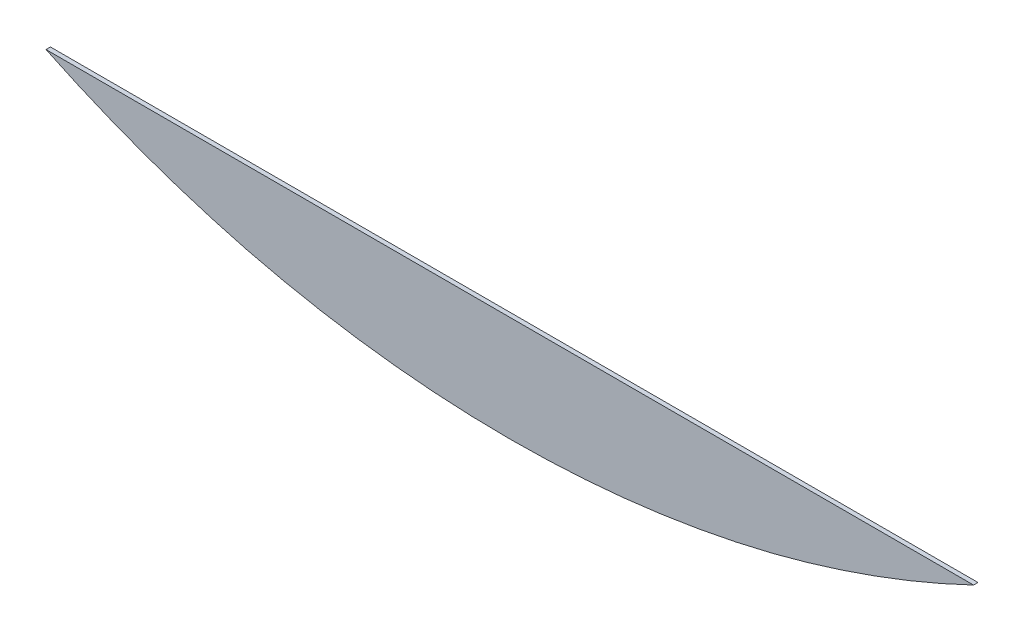
SolidWorks part; units mm, degrees
ref_plane "Front Plane" through (0, 0, 0) normal (0, 0, 1) x (1, 0, 0)
ref_plane "Top Plane" through (0, 0, 0) normal (0, 1, 0) x (1, 0, 0)
ref_plane "Right Plane" through (0, 0, 0) normal (1, 0, 0) x (0, 0, -1)
sketch "Sketch1" plane through (0, 0, 0) normal (0, 0, 1) x (1, 0, 0)
  line L0 (0, 0) -> (670.56, 0)
  line L1 (144.78, -52.6831) -> (144.78, 0) construction
  line L2 (335.28, 0) -> (335.28, -76.2) construction
  line L3 (525.78, -52.6831) -> (525.78, 0) construction
  arc A0 (0, 0) -> (144.78, -52.6831) centre (338.9521, 706.2059) ccw
  arc A1 (670.56, 0) -> (525.78, -52.6831) centre (331.6079, 706.2059) cw
  arc A2 (144.78, -52.6831) -> (525.78, -52.6831) centre (335.28, 707.136) ccw
  dimension "D1" = 783.336
  dimension "D2" = 670.56
  dimension "D3" = 381
  dimension "D4" = 76.2
extrude "Boss-Extrude1" add sketch "Sketch1" along normal blind 3.2004
